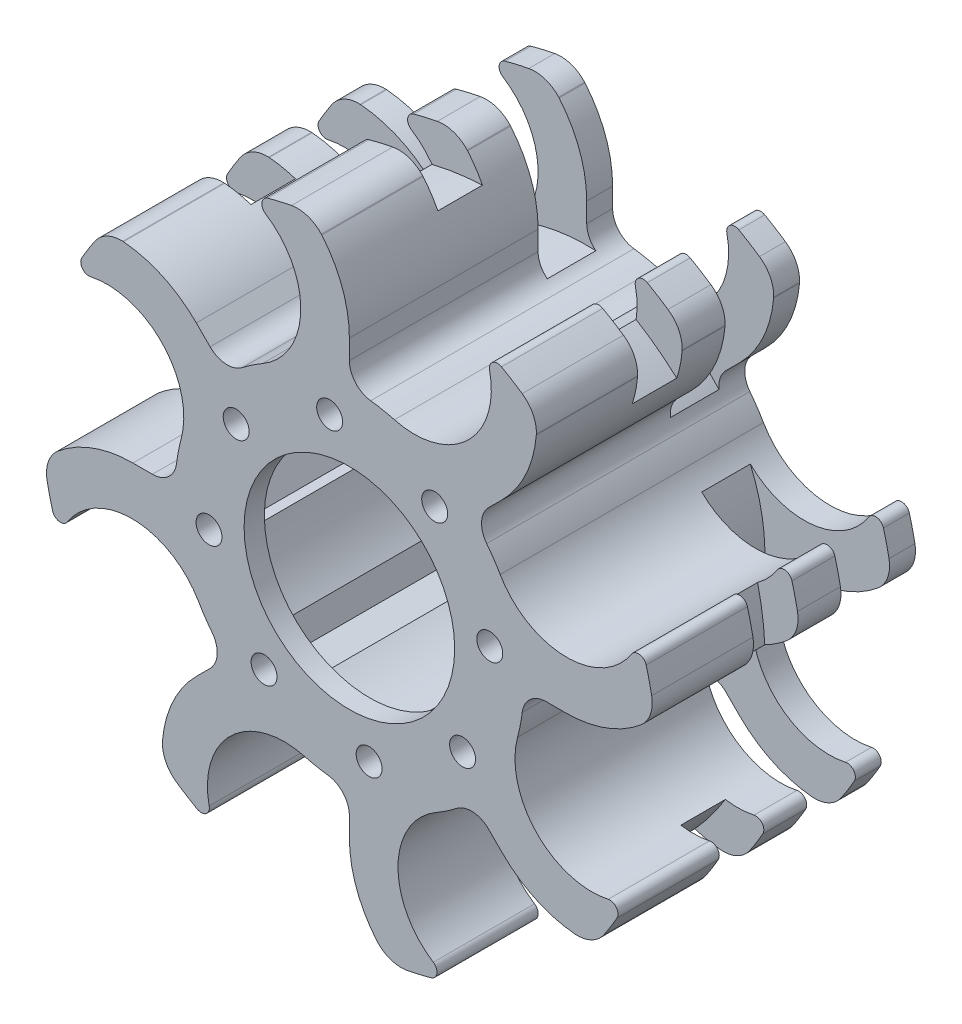
SolidWorks part; units mm, degrees
ref_plane "前视基准面" through (0, 0, 0) normal (0, 0, 1) x (1, 0, 0)
ref_plane "上视基准面" through (0, 0, 0) normal (0, 1, 0) x (1, 0, 0)
ref_plane "右视基准面" through (0, 0, 0) normal (1, 0, 0) x (0, 0, -1)
sketch "草图1" plane through (0, 0, 0) normal (0, 0, 1) x (1, 0, 0)
  line L0 (0, 0) -> (50000, 0) construction
  line L1 (0, 0) -> (0, -50000) construction
  line L2 (0, 0) -> (-10.75, 18.6195) construction
  line L3 (0, 21.5) -> (0, 26.7215)
  line L4 (-3.4, 36.0376) -> (32202.7815, -38210.0324) construction
  circle A0 centre (0, 0) radius 21.5
  arc A1 (0, 26.7215) -> (-3.4, 36.0376) centre (-14.4632, 26.7215) ccw
  arc A2 (-3.4, 36.0376) -> (-3.4606, 36.1064) centre (-4.9298, 34.7494) ccw
  arc A3 (-3.4606, 36.1064) -> (-7.1519, 37.3209) centre (-6.3991, 33.3924) ccw
  circle A4 centre (0, 0) radius 38 construction
  arc A5 (-7.1519, 37.3209) -> (-10.0801, 36.6387) centre (0, 0) ccw
  arc A6 (-10.0801, 36.6387) -> (-10.7994, 35.4998) centre (-9.8148, 35.6745) ccw
  arc A7 (-10.7994, 35.4998) -> (-10.3562, 34.8338) centre (-9.8148, 35.6745) ccw
  arc A8 (-10.3562, 34.8338) -> (-10.75, 18.6195) centre (-15.5, 26.8468) cw
  point P29 (0, 32)
  dimension "D1" = 43
  dimension "D3" = 76
  dimension "D5" = 2
  dimension "D6" = 4
  dimension "D7" = 40.1
  dimension "D8" = 1
  dimension "D9" = 1
  dimension "D11" = 9.5
  dimension "D2" = 30
  dimension "D4" = 3.4
  dimension "D10" = 0.8
  dimension "D12" = 32
extrude "凸台-拉伸1" add sketch "草图1" along normal blind 32.5 contours A7 A8 A0 L3 A1 A2 A3 A5 A6 | A0 A5
pattern_circular "阵列(圆周)1" count 8 over 360 about axis through (0, 0, 0) along (0, 0, 1) of "凸台-拉伸1"
fillet "圆角1" radius 3 8 edges at (15.2028, 15.2028, 16.25) (21.5, 0, 16.25) (15.2028, -15.2028, 16.25) (0, -21.5, 16.25) (-15.2028, -15.2028, 16.25) (-21.5, 0, 16.25) (-15.2028, 15.2028, 16.25) (0, 21.5, 16.25)
sketch "草图3" plane through (0, 0, 0) normal (0, 0, -1) x (-1, 0, 0)
  circle A0 centre (0, 0) radius 18.5
  dimension "D1" = 37
extrude "切除-拉伸1" cut sketch "草图3" against normal offset from surface (30 mm away) 2.5 up to face at (0, 0, 32.5)
sketch "草图4" plane through (0, 0, 32.5) normal (0, 0, 1) x (1, 0, 0)
  line L0 (0, 0) -> (50000, 0) construction
  line L1 (0, 0) -> (0, -50000) construction
  line L2 (-2.4355, 17.3297) -> (0, 0) construction
  circle A0 centre (0, 0) radius 17.5 construction
  circle A1 centre (-2.4355, 17.3297) radius 1.6
  circle A7 centre (0, 0) radius 13
  circle A8 centre (10.5318, 13.9761) radius 1.6
  circle A9 centre (17.3297, 2.4355) radius 1.6
  circle A10 centre (13.9761, -10.5318) radius 1.6
  circle A11 centre (2.4355, -17.3297) radius 1.6
  circle A12 centre (-10.5318, -13.9761) radius 1.6
  circle A13 centre (-17.3297, -2.4355) radius 1.6
  circle A14 centre (-13.9761, 10.5318) radius 1.6
  point P22 (0, 0)
  point P28 (0, 0)
  dimension "D1" = 35
  dimension "D2" = 3.2
  dimension "D5" = 26
  dimension "D3" = 8
  dimension "D4" = 8
extrude "切除-拉伸2" cut sketch "草图4" against normal blind 2.5
sketch "草图6" plane through (0, 0, 30) normal (0, 0, -1) x (-1, 0, 0)
  line L0 (2.4355, 20.6206) -> (2.4355, 14.0388) construction
  line L1 (2.4355, 20.6206) -> (-0.4145, 18.9751)
  line L2 (-0.4145, 18.9751) -> (-0.4145, 15.6842)
  line L3 (-0.4145, 15.6842) -> (2.4355, 14.0388)
  line L4 (2.4355, 14.0388) -> (5.2855, 15.6842)
  line L5 (5.2855, 15.6842) -> (5.2855, 18.9751)
  line L6 (5.2855, 18.9751) -> (2.4355, 20.6206)
  line L7 (16.3031, 12.8588) -> (13.1244, 13.7105)
  line L8 (13.1244, 13.7105) -> (10.7974, 11.3835)
  line L9 (10.7974, 11.3835) -> (11.6491, 8.2047)
  line L10 (11.6491, 8.2047) -> (14.8279, 7.353)
  line L11 (14.8279, 7.353) -> (17.1549, 9.68)
  line L12 (17.1549, 9.68) -> (16.3031, 12.8588)
  line L13 (20.6206, -2.4355) -> (18.9751, 0.4145)
  line L14 (18.9751, 0.4145) -> (15.6842, 0.4145)
  line L15 (15.6842, 0.4145) -> (14.0388, -2.4355)
  line L16 (14.0388, -2.4355) -> (15.6842, -5.2855)
  line L17 (15.6842, -5.2855) -> (18.9751, -5.2855)
  line L18 (18.9751, -5.2855) -> (20.6206, -2.4355)
  line L19 (12.8588, -16.3031) -> (13.7105, -13.1244)
  line L20 (13.7105, -13.1244) -> (11.3835, -10.7974)
  line L21 (11.3835, -10.7974) -> (8.2047, -11.6491)
  line L22 (8.2047, -11.6491) -> (7.353, -14.8279)
  line L23 (7.353, -14.8279) -> (9.68, -17.1549)
  line L24 (9.68, -17.1549) -> (12.8588, -16.3031)
  line L25 (-2.4355, -20.6206) -> (0.4145, -18.9751)
  line L26 (0.4145, -18.9751) -> (0.4145, -15.6842)
  line L27 (0.4145, -15.6842) -> (-2.4355, -14.0388)
  line L28 (-2.4355, -14.0388) -> (-5.2855, -15.6842)
  line L29 (-5.2855, -15.6842) -> (-5.2855, -18.9751)
  line L30 (-5.2855, -18.9751) -> (-2.4355, -20.6206)
  line L31 (-16.3031, -12.8588) -> (-13.1244, -13.7105)
  line L32 (-13.1244, -13.7105) -> (-10.7974, -11.3835)
  line L33 (-10.7974, -11.3835) -> (-11.6491, -8.2047)
  line L34 (-11.6491, -8.2047) -> (-14.8279, -7.353)
  line L35 (-14.8279, -7.353) -> (-17.1549, -9.68)
  line L36 (-17.1549, -9.68) -> (-16.3031, -12.8588)
  line L37 (-20.6206, 2.4355) -> (-18.9751, -0.4145)
  line L38 (-18.9751, -0.4145) -> (-15.6842, -0.4145)
  line L39 (-15.6842, -0.4145) -> (-14.0388, 2.4355)
  line L40 (-14.0388, 2.4355) -> (-15.6842, 5.2855)
  line L41 (-15.6842, 5.2855) -> (-18.9751, 5.2855)
  line L42 (-18.9751, 5.2855) -> (-20.6206, 2.4355)
  line L43 (-12.8588, 16.3031) -> (-13.7105, 13.1244)
  line L44 (-13.7105, 13.1244) -> (-11.3835, 10.7974)
  line L45 (-11.3835, 10.7974) -> (-8.2047, 11.6491)
  line L46 (-8.2047, 11.6491) -> (-7.353, 14.8279)
  line L47 (-7.353, 14.8279) -> (-9.68, 17.1549)
  line L48 (-9.68, 17.1549) -> (-12.8588, 16.3031)
  circle A0 centre (2.4355, 17.3297) radius 2.85 construction
  point P54 (0, 0)
  dimension "D1" = 5.7
  dimension "D2" = 8
extrude "切除-拉伸4" cut sketch "草图6" along normal up to next
sketch "草图7" plane through (0, 0, 0) normal (0, 1, 0) x (1, 0, 0)
  line L0 (34.8338, 0) -> (18.6195, 0) construction
  line L1 (22, -9.2) -> (42, -9.2)
  line L2 (22, -9.2) -> (22, -3.2)
  line L3 (22, -3.2) -> (42, -3.2)
  line L4 (42, -9.2) -> (42, -3.2)
  line L5 (22, -9.2) -> (42, -3.2) construction
  line L6 (22, -3.2) -> (42, -9.2) construction
  line L7 (0, 0) -> (0, 50000) construction
  line L8 (37.3209, -32.5) -> (37.3209, 0) construction
  line L9 (33.3209, -20) -> (43.3209, -20)
  line L10 (33.3209, -20) -> (33.3209, -14.5)
  line L11 (33.3209, -14.5) -> (43.3209, -14.5)
  line L12 (43.3209, -20) -> (43.3209, -14.5)
  line L13 (33.3209, -20) -> (43.3209, -14.5) construction
  line L14 (33.3209, -14.5) -> (43.3209, -20) construction
  point P0 (32, -6.2)
  point P11 (38.3209, -17.25)
  dimension "D1" = 3.2
  dimension "D2" = 22
  dimension "D3" = 6
  dimension "D4" = 20
  dimension "D5" = 12.5
  dimension "D6" = 4
  dimension "D7" = 10
  dimension "D8" = 5.5
revolve "切除-旋转1" cut sketch "草图7" angle 360 about L7
